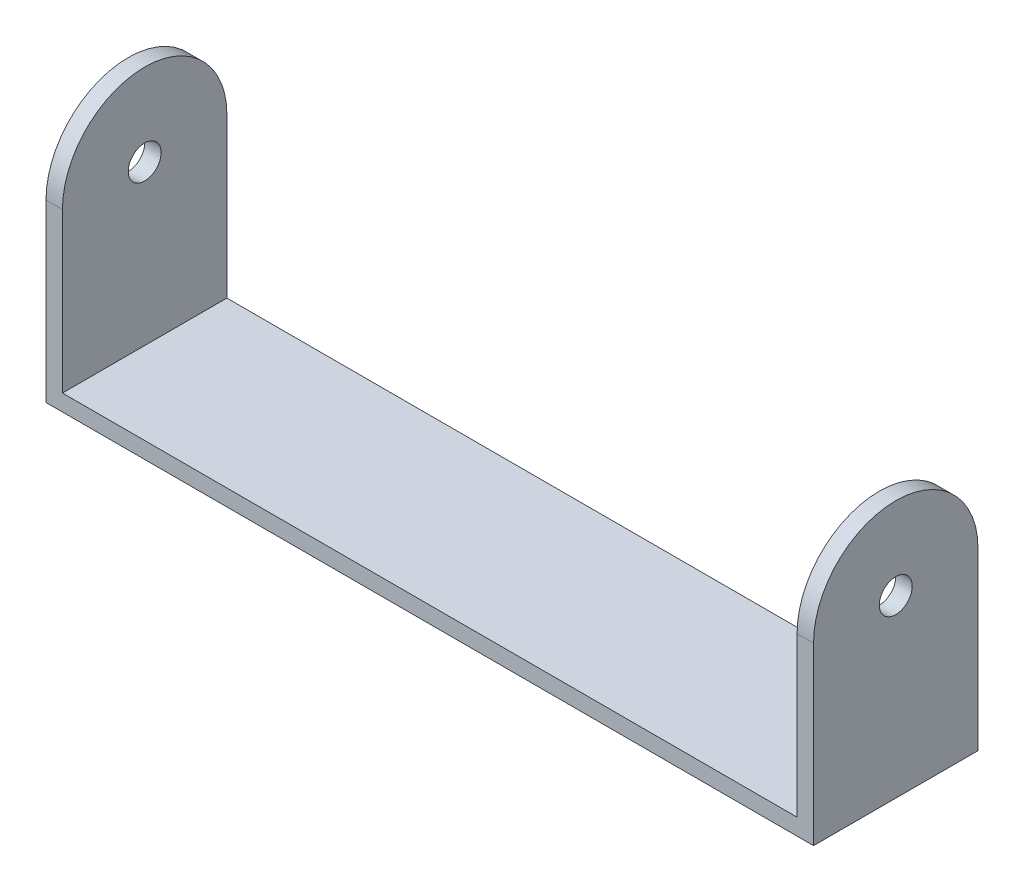
SolidWorks part; units mm, degrees
ref_plane "Front Plane" through (0, 0, 0) normal (0, 0, 1) x (1, 0, 0)
ref_plane "Top Plane" through (0, 0, 0) normal (0, 1, 0) x (1, 0, 0)
ref_plane "Right Plane" through (0, 0, 0) normal (1, 0, 0) x (0, 0, -1)
sketch "Sketch1" plane through (0, 0, 0) normal (0, 1, 0) x (1, 0, 0)
  line L1 (-35, 7.5) -> (35, 7.5)
  line L2 (-35, 7.5) -> (-35, -7.5)
  line L3 (-35, -7.5) -> (35, -7.5)
  line L4 (35, 7.5) -> (35, -7.5)
  line L5 (-35, 7.5) -> (35, -7.5) construction
  line L6 (-35, -7.5) -> (35, 7.5) construction
  point P0 (0, 0)
extrude "Boss-Extrude1" add sketch "Sketch1" along normal blind 1.5
sketch "Sketch2" plane through (0, 1.5, 0) normal (0, 1, 0) x (1, 0, 0)
  line L0 (-35, 7.5) -> (-35, -7.5)
  line L1 (-35, 7.5) -> (-35, -7.5) construction
  line L2 (-35, -7.5) -> (-33.5, -7.5)
  line L3 (-35, -7.5) -> (35, -7.5) construction
  line L4 (-33.5, -7.5) -> (-33.5, 7.5)
  line L5 (35, 7.5) -> (-35, 7.5) construction
  line L6 (-33.5, 7.5) -> (-35, 7.5)
  line L7 (35, 7.5) -> (33.5, 7.5)
  line L8 (33.5, 7.5) -> (33.5, -7.5)
  line L9 (33.5, -7.5) -> (35, -7.5)
  line L10 (35, -7.5) -> (35, 7.5)
extrude "Boss-Extrude2" add sketch "Sketch2" along normal blind 22
sketch "Sketch3" plane through (-35, 0, 0) normal (-1, 0, 0) x (0, 0, 1)
  line L0 (0, 23.5) -> (0, 16) construction
  line L1 (-7.5, 23.5) -> (7.5, 23.5) construction
  line L2 (-7.5, 16) -> (-7.5, 23.5)
  line L3 (-7.5, 23.5) -> (7.5, 23.5)
  line L4 (7.5, 23.5) -> (7.5, 16)
  arc A0 (7.5, 16) -> (-7.5, 16) centre (0, 16) ccw
  circle A1 centre (0, 16) radius 1.5
extrude "Cut-Extrude1" cut sketch "Sketch3" against normal through all
